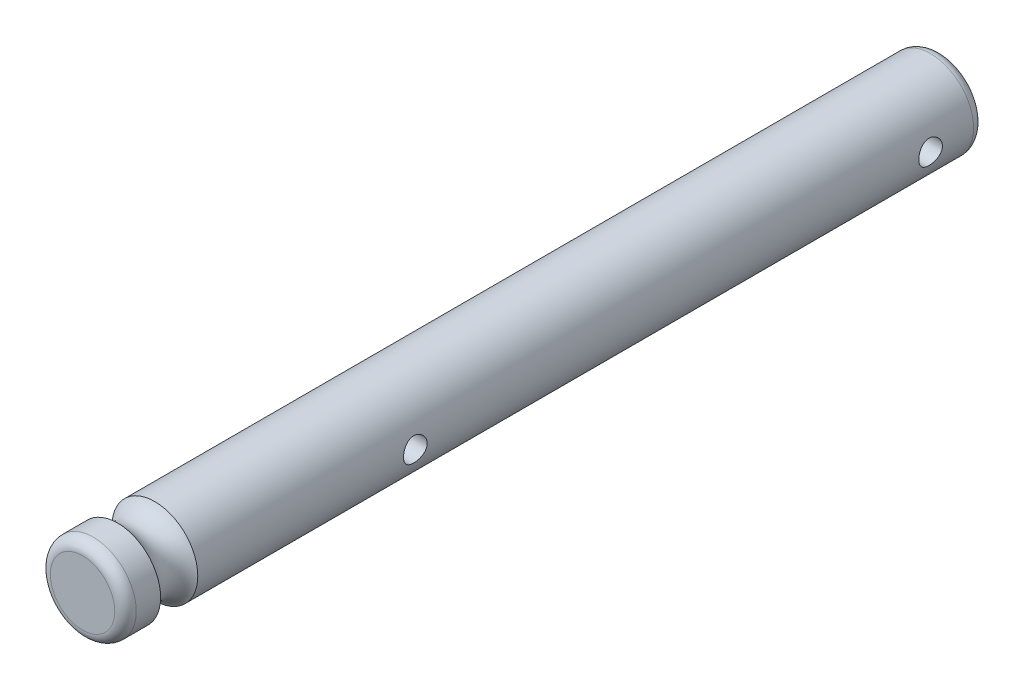
SolidWorks part; units mm, degrees
ref_plane "Front Plane" through (0, 0, 0) normal (0, 0, 1) x (1, 0, 0)
ref_plane "Top Plane" through (0, 0, 0) normal (0, 1, 0) x (1, 0, 0)
ref_plane "Right Plane" through (0, 0, 0) normal (1, 0, 0) x (0, 0, -1)
sketch "Sketch1" plane through (0, 0, 0) normal (0, 0, 1) x (1, 0, 0)
  circle A0 centre (27.8586, 100.8262) radius 2 construction
  circle A1 centre (27.8586, 100.8262) radius 2
extrude "Boss-Extrude1" add sketch "Sketch1" against normal blind 35
sketch "Sketch2" plane through (0, 0, 0) normal (0, 0, 1) x (1, 0, 0)
  circle A1 centre (27.8586, 100.8262) radius 2
  circle A3 centre (27.8586, 100.8262) radius 2
  dimension "D1" = 0
extrude "Boss-Extrude2" add sketch "Sketch2" along normal blind 5
ref_plane "Plane1" through (27.8586, 0, 0) normal (1, 0, 0) x (0, 0, -1)
sketch "Sketch3" plane through (27.8586, 0, 0) normal (1, 0, 0) x (0, 0, -1)
  line L1 (-5, 130.4055) -> (0, 130.4055) construction
  circle A0 centre (-2.5, 103.3262) radius 1
  point P8 (-2.5, 130.4055)
  dimension "D1" = 2
  dimension "D2" = 0.5
revolve "Cut-Revolve1" cut sketch "Sketch3" angle 360 about axis through (27.8586, 100.8262, -35) along (0, 0, 1)
fillet "Fillet1" radius 0.5 2 edges at (29.8586, 100.8262, -35) (29.8586, 100.8262, 5)
sketch "Sketch4" plane through (0, 0, 0) normal (1, 0, 0) x (0, 0, -1)
  line L0 (34.5, 100.8262) -> (-1.634, 100.8262) construction
  line L1 (34.5, 102.8262) -> (34.5, 98.8262) construction
  circle A0 centre (32.5, 100.8262) radius 0.55
  circle A1 centre (8.5, 100.8262) radius 0.55
  dimension "D1" = 1.1
  dimension "D2" = 2
  dimension "D3" = 24
extrude "Cut-Extrude1" cut sketch "Sketch4" against normal through all both and the other way through all
